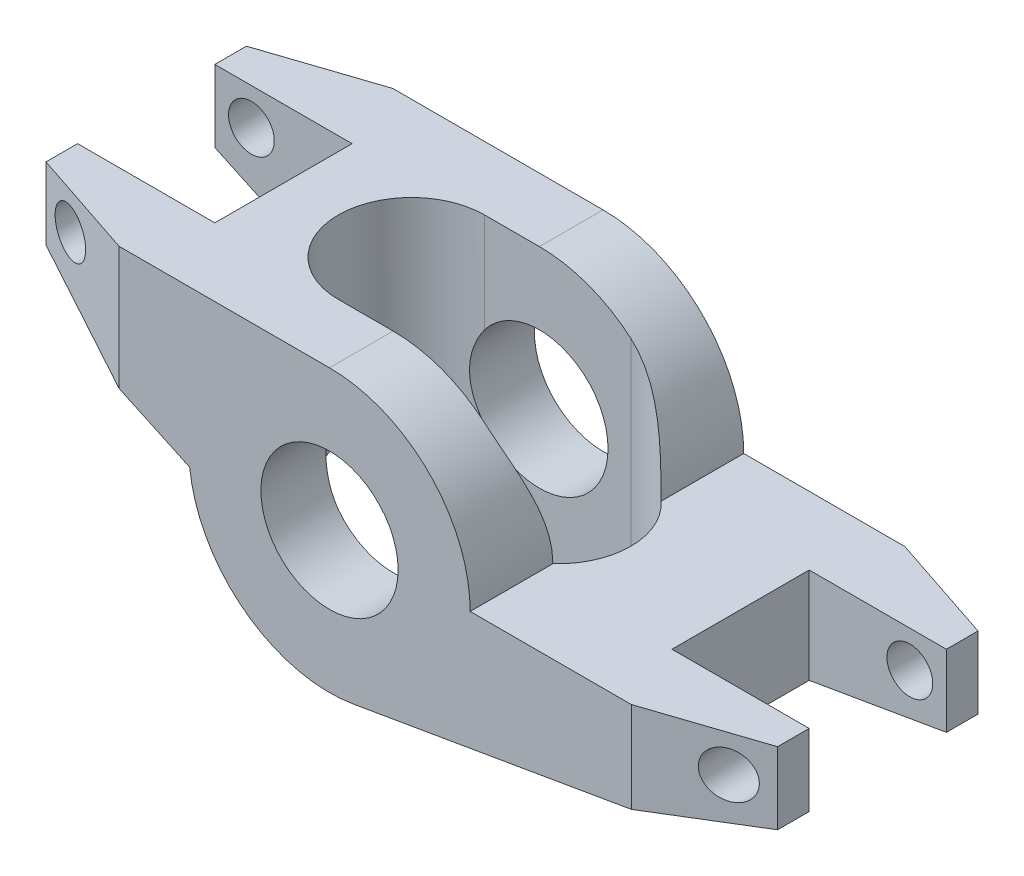
SolidWorks part; units mm, degrees
ref_plane "Front Plane" through (0, 0, 0) normal (0, 0, 1) x (1, 0, 0)
ref_plane "Top Plane" through (0, 0, 0) normal (0, 1, 0) x (1, 0, 0)
ref_plane "Right Plane" through (0, 0, 0) normal (1, 0, 0) x (0, 0, -1)
sketch "Sketch1" plane through (0, 0, 0) normal (0, 0, 1) x (1, 0, 0)
  line L0 (0, 9.77) -> (-22.23, 9.77)
  line L1 (-22.23, 9.77) -> (-22.23, 4.77)
  line L2 (-22.23, 4.77) -> (-9.7115, -1.0675)
  line L3 (9.77, 0) -> (28.58, 0)
  line L4 (28.58, 0) -> (28.58, -5)
  line L5 (28.58, -5) -> (1.6553, -9.6287)
  arc A0 (-9.7115, -1.0675) -> (1.6553, -9.6287) centre (0, 0) ccw
  circle A1 centre (0, 0) radius 4.765
  arc A2 (9.77, 0) -> (0, 9.77) centre (0, 0) ccw
  point P10 (0, 0)
  dimension "D1" = 9.53
  dimension "D2" = 19.54
  dimension "D3" = 5
  dimension "D4" = 22.23
  dimension "D5" = 25
  dimension "D6" = 28.58
extrude "Boss-Extrude1" add sketch "Sketch1" along normal mid plane 19
chamfer "Chamfer1" distance 7.62 distance2 2.54 2 edges at (-22.23, 7.27, -9.5) (28.58, -2.5, -9.5)
chamfer "Chamfer2" distance 2.54 distance2 7.62 2 edges at (-22.23, 7.27, 9.5) (28.58, -2.5, 9.5)
sketch "Sketch5" plane through (0, 9.77, 0) normal (0, 1, 0) x (1, 0, 0)
  line L0 (-22.23, -6.96) -> (-22.23, 6.96) construction
  line L1 (-22.23, 4.765) -> (-12.7, 4.765)
  line L2 (-22.23, 4.765) -> (-22.23, -4.765)
  line L3 (-22.23, -4.765) -> (-12.7, -4.765)
  line L4 (-12.7, 4.765) -> (-12.7, -4.765)
  line L5 (28.58, -6.96) -> (28.58, 6.96) construction
  line L6 (28.58, 4.765) -> (19.05, 4.765)
  line L7 (28.58, 4.765) -> (28.58, -4.765)
  line L8 (28.58, -4.765) -> (19.05, -4.765)
  line L9 (19.05, 4.765) -> (19.05, -4.765)
  point P12 (-22.23, 0)
  point P14 (19.05, 0)
  dimension "D1" = 9.53
extrude "Cut-Extrude1" cut sketch "Sketch5" against normal through all
sketch "Sketch6" plane through (0, 0, 0) normal (0, 1, 0) x (1, 0, 0)
  line L0 (-3.81, 0) -> (6.35, 0) construction
  line L1 (-3.81, 5.08) -> (6.35, 5.08)
  line L2 (-3.81, -5.08) -> (6.35, -5.08)
  line L3 (-12.7, -4.765) -> (-12.7, 4.765) construction
  arc A0 (-3.81, 5.08) -> (-3.81, -5.08) centre (-3.81, 0) ccw
  arc A1 (6.35, -5.08) -> (6.35, 5.08) centre (6.35, 0) ccw
  point P3 (1.27, 0)
  dimension "D2" = 5.08
  dimension "D1" = 8.89
  dimension "D3" = 10.16
extrude "Cut-Extrude2" cut sketch "Sketch6" against normal through all both and the other way through all
sketch "Sketch7" plane through (0, 0, 0) normal (0, 0, 1) x (1, 0, 0)
  line L0 (-22.23, 9.77) -> (-14.61, 9.77) construction
  line L1 (20.96, 0) -> (28.58, 0) construction
  line L2 (28.58, 0) -> (28.58, -5) construction
  line L3 (-22.23, 4.77) -> (-22.23, 9.77) construction
  circle A0 centre (-19.69, 7.23) radius 1.59
  circle A1 centre (26.04, -2.54) radius 1.59
  dimension "D1" = 3.18
  dimension "D2" = 2.54
  dimension "D3" = 2.54
  dimension "D4" = 2.54
  dimension "D5" = 2.54
extrude "Cut-Extrude3" cut sketch "Sketch7" against normal through all both and the other way through all
